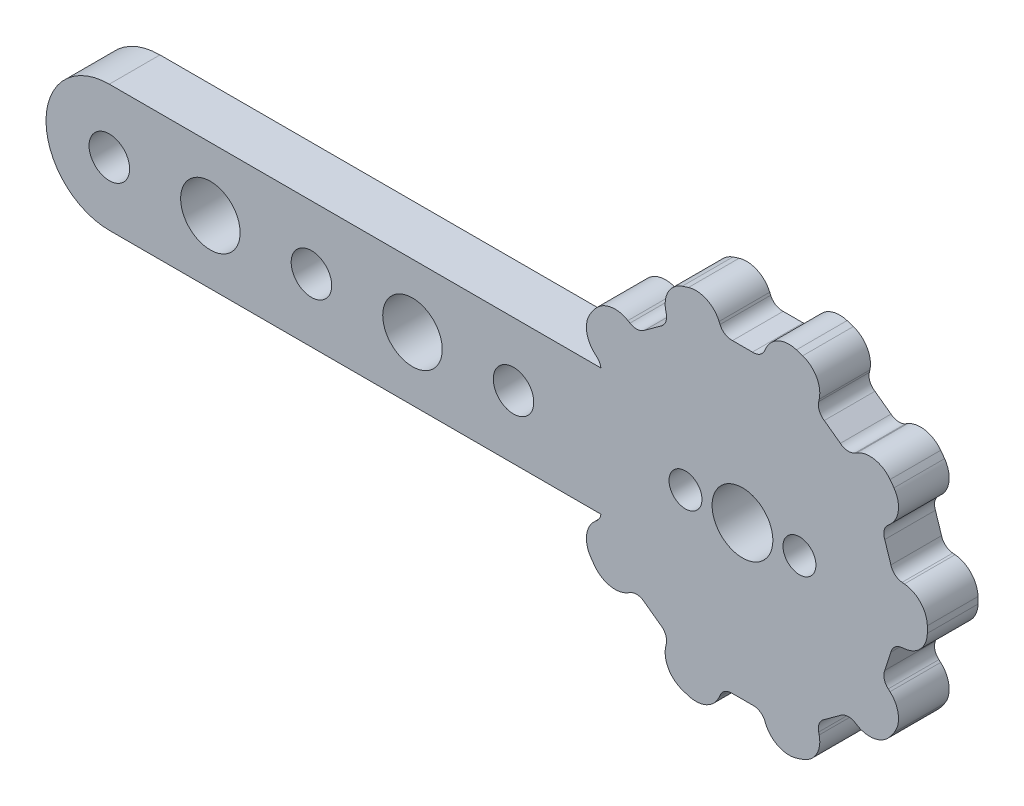
SolidWorks part; units mm, degrees
ref_plane "Front Plane" through (0, 0, 0) normal (0, 0, 1) x (1, 0, 0)
ref_plane "Top Plane" through (0, 0, 0) normal (0, 1, 0) x (1, 0, 0)
ref_plane "Right Plane" through (0, 0, 0) normal (1, 0, 0) x (0, 0, -1)
sketch "Sketch1" plane through (0, 0, 0) normal (0, 0, 1) x (1, 0, 0)
  line L0 (6.4582, 10.2265) -> (7.7303, 9.3022)
  line L1 (-1.5, 0) -> (-1.5, 24.9517) construction
  line L2 (11.2358, 4.4774) -> (11.7217, 2.9819)
  line L3 (0, 0) -> (0, 24.9517) construction
  line L4 (11.7217, -2.9819) -> (11.2358, -4.4774)
  line L5 (0, 0) -> (0, 2.4) construction
  line L6 (1.5, 0) -> (1.5, 1.8735) construction
  line L7 (-1.5, 0) -> (-1.5, 1.8735) construction
  line L8 (1.5, 0) -> (1.5, 24.9517) construction
  line L9 (7.7303, -9.3022) -> (6.4582, -10.2265)
  line L10 (0.7862, -12.0694) -> (-0.7862, -12.0694)
  line L11 (-6.4582, -10.2265) -> (-7.7303, -9.3022)
  line L12 (-11.2358, -4.4774) -> (-11.7217, -2.9819)
  line L13 (-11.7217, 2.9819) -> (-11.2358, 4.4774)
  line L14 (-7.7303, 9.3022) -> (-6.4582, 10.2265)
  line L15 (-0.7862, 12.0694) -> (0.7862, 12.0694)
  line L16 (0, 0) -> (-4.5, 0) construction
  line L17 (0, 0) -> (4.5, 0) construction
  circle A0 centre (0, 0) radius 2.4
  circle A4 centre (0, 0) radius 14.5 construction
  arc A5 (12.867, -6.8994) -> (11.509, -5.6025) centre (-1.545, -20.6319) ccw
  arc A6 (10.5378, -10.1052) -> (8.8848, -9.2144) centre (19.1447, 7.8449) cw
  arc A7 (10.5378, -10.1052) -> (12.867, -6.8994) centre (0, 0) ccw
  arc A8 (7.7303, -9.3022) -> (8.8848, -9.2144) centre (8.3694, -10.0713) cw
  arc A9 (11.2358, -4.4774) -> (11.509, -5.6025) centre (12.1647, -4.8476) ccw
  arc A10 (6.3543, -13.1447) -> (6.0179, -11.2974) centre (-13.377, -15.7834) ccw
  arc A11 (2.5856, -14.3692) -> (1.7719, -12.677) centre (20.0995, -4.9063) cw
  arc A12 (2.5856, -14.3692) -> (6.3543, -13.1447) centre (0, 0) ccw
  arc A13 (0.7862, -12.0694) -> (1.7719, -12.677) centre (0.8512, -13.0673) cw
  arc A14 (6.4582, -10.2265) -> (6.0179, -11.2974) centre (6.9921, -11.072) ccw
  arc A15 (14.4649, 1.9813) -> (12.604, 2.2322) centre (10.8772, -17.5996) ccw
  arc A16 (14.4649, -1.9813) -> (12.604, -2.2322) centre (10.8772, 17.5996) cw
  arc A17 (14.4649, -1.9813) -> (14.4649, 1.9813) centre (0, 0) ccw
  arc A18 (11.7217, -2.9819) -> (12.604, -2.2322) centre (12.6908, -3.2285) cw
  arc A19 (11.7217, 2.9819) -> (12.604, 2.2322) centre (12.6908, 3.2285) ccw
  circle A21 centre (4.5, 0) radius 1.3
  circle A22 centre (-4.5, 0) radius 1.3
  arc A27 (-2.5856, -14.3692) -> (-1.7719, -12.677) centre (-20.0995, -4.9063) ccw
  arc A28 (-6.3543, -13.1447) -> (-6.0179, -11.2974) centre (13.377, -15.7834) cw
  arc A29 (-6.3543, -13.1447) -> (-2.5856, -14.3692) centre (0, 0) ccw
  arc A30 (-6.4582, -10.2265) -> (-6.0179, -11.2974) centre (-6.9921, -11.072) cw
  arc A31 (-0.7862, -12.0694) -> (-1.7719, -12.677) centre (-0.8512, -13.0673) ccw
  arc A32 (-10.5378, -10.1052) -> (-8.8848, -9.2144) centre (-19.1447, 7.8449) ccw
  arc A33 (-12.867, -6.8994) -> (-11.509, -5.6025) centre (1.545, -20.6319) cw
  arc A34 (-12.867, -6.8994) -> (-10.5378, -10.1052) centre (0, 0) ccw
  arc A35 (-11.2358, -4.4774) -> (-11.509, -5.6025) centre (-12.1647, -4.8476) cw
  arc A36 (-7.7303, -9.3022) -> (-8.8848, -9.2144) centre (-8.3694, -10.0713) ccw
  arc A37 (-14.4649, -1.9813) -> (-12.604, -2.2322) centre (-10.8772, 17.5996) ccw
  arc A38 (-14.4649, 1.9813) -> (-12.604, 2.2322) centre (-10.8772, -17.5996) cw
  arc A39 (-14.4649, 1.9813) -> (-14.4649, -1.9813) centre (0, 0) ccw
  arc A40 (-11.7217, 2.9819) -> (-12.604, 2.2322) centre (-12.6908, 3.2285) cw
  arc A41 (-11.7217, -2.9819) -> (-12.604, -2.2322) centre (-12.6908, -3.2285) ccw
  arc A42 (-12.867, 6.8994) -> (-11.509, 5.6025) centre (1.545, 20.6319) ccw
  arc A43 (-10.5378, 10.1052) -> (-8.8848, 9.2144) centre (-19.1447, -7.8449) cw
  arc A44 (-10.5378, 10.1052) -> (-12.867, 6.8994) centre (0, 0) ccw
  arc A45 (-7.7303, 9.3022) -> (-8.8848, 9.2144) centre (-8.3694, 10.0713) cw
  arc A46 (-11.2358, 4.4774) -> (-11.509, 5.6025) centre (-12.1647, 4.8476) ccw
  arc A47 (-6.3543, 13.1447) -> (-6.0179, 11.2974) centre (13.377, 15.7834) ccw
  arc A48 (-2.5856, 14.3692) -> (-1.7719, 12.677) centre (-20.0995, 4.9063) cw
  arc A49 (-2.5856, 14.3692) -> (-6.3543, 13.1447) centre (0, 0) ccw
  arc A50 (-0.7862, 12.0694) -> (-1.7719, 12.677) centre (-0.8512, 13.0673) cw
  arc A51 (-6.4582, 10.2265) -> (-6.0179, 11.2974) centre (-6.9921, 11.072) ccw
  arc A52 (2.5856, 14.3692) -> (1.7719, 12.677) centre (20.0995, 4.9063) ccw
  arc A53 (6.3543, 13.1447) -> (6.0179, 11.2974) centre (-13.377, 15.7834) cw
  arc A54 (6.3543, 13.1447) -> (2.5856, 14.3692) centre (0, 0) ccw
  arc A55 (6.4582, 10.2265) -> (6.0179, 11.2974) centre (6.9921, 11.072) cw
  arc A56 (0.7862, 12.0694) -> (1.7719, 12.677) centre (0.8512, 13.0673) ccw
  arc A57 (10.5378, 10.1052) -> (8.8848, 9.2144) centre (19.1447, -7.8449) ccw
  arc A58 (12.867, 6.8994) -> (11.509, 5.6025) centre (-1.545, 20.6319) cw
  arc A59 (12.867, 6.8994) -> (10.5378, 10.1052) centre (0, 0) ccw
  arc A60 (11.2358, 4.4774) -> (11.509, 5.6025) centre (12.1647, 4.8476) cw
  arc A61 (7.7303, 9.3022) -> (8.8848, 9.2144) centre (8.3694, 10.0713) ccw
  point P44 (-19.23, 0.4774)
  point P131 (0, 0)
  point P151 (0, 0)
  dimension "D1" = 4.8
  dimension "D2" = 10
  dimension "D3" = 9
  dimension "D5" = 10
  dimension "D6" = 29
  dimension "D7" = 1
  dimension "D4" = 2.6
  dimension "D14" = 14.6
  dimension "D11" = 1.5
  dimension "D12" = 1.5
extrude "Boss-Extrude1" add sketch "Sketch1" along normal blind 4
sketch "Sketch2" plane through (0, 0, 0) normal (0, 0, -1) x (-1, 0, 0)
  line L0 (0, 0) -> (50, 0) construction
  line L4 (9.0126, 0) -> (9.0126, 5)
  line L5 (9.0126, 5) -> (50, 5)
  line L6 (9.0126, 0) -> (9.0126, -5)
  line L7 (9.0126, -5) -> (50, -5)
  circle A0 centre (50, 0) radius 1.6
  arc A2 (50, 5) -> (50, -5) centre (50, 0) cw
  circle A3 centre (42.02, 0) radius 2.35
  circle A4 centre (34.04, 0) radius 1.6
  circle A5 centre (26.06, 0) radius 2.35
  circle A6 centre (18.08, 0) radius 1.6
  dimension "D1" = 3.2
  dimension "D5" = 3.2
  dimension "D10" = 4.7
  dimension "D11" = 4.7
  dimension "D12" = 3.2
  dimension "D2" = 50
  dimension "D3" = 5
  dimension "D4" = 5
  dimension "D6" = 7.98
  dimension "D7" = 7.98
  dimension "D8" = 7.98
  dimension "D9" = 7.98
extrude "Boss-Extrude2" add sketch "Sketch2" along normal blind 4 from surface at -4 starting at face at (0, 0, 4)
fillet "Fillet1" radius 2 18 edges at (-12.867, -6.8994, 2) (14.4649, 1.9813, 2) (12.867, -6.8994, 2) (6.3543, -13.1447, 2) (-2.5856, -14.3692, 2) (-10.5378, -10.1052, 2) (-6.3543, -13.1447, 2) (2.5856, -14.3692, 2) (10.5378, -10.1052, 2) (14.4649, -1.9813, 2) (12.867, 6.8994, 2) (10.5378, 10.1052, 2) (2.5856, 14.3692, 2) (6.3543, 13.1447, 2) (-2.5856, 14.3692, 2) (-6.3543, 13.1447, 2) (-10.5378, 10.1052, 2) (-12.867, 6.8994, 2)
